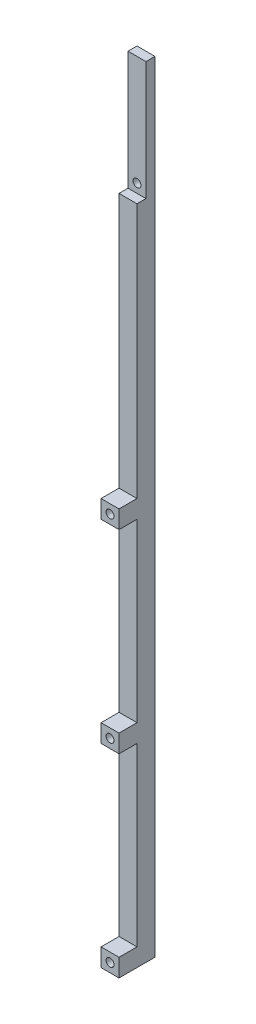
SolidWorks part; units mm, degrees
ref_plane "Front Plane" through (0, 0, 0) normal (0, 0, 1) x (1, 0, 0)
ref_plane "Top Plane" through (0, 0, 0) normal (0, 1, 0) x (1, 0, 0)
ref_plane "Right Plane" through (0, 0, 0) normal (1, 0, 0) x (0, 0, -1)
sketch "Sketch1" plane through (0, 0, 0) normal (0, 1, 0) x (1, 0, 0)
  line L1 (0, 0) -> (6.35, 0)
  line L2 (0, 0) -> (0, 12.7)
  line L3 (0, 12.7) -> (6.35, 12.7)
  line L4 (6.35, 0) -> (6.35, 12.7)
  dimension "D1" = 6.35
  dimension "D2" = 12.7
extrude "Boss-Extrude1" add sketch "Sketch1" along normal blind 275.59
sketch "Sketch2" plane through (0, 0, 0) normal (-1, 0, 0) x (0, 0, 1)
  line L0 (0, 275.59) -> (0, 0) construction
  line L1 (0, 275.59) -> (-9.525, 275.59)
  line L2 (0, 275.59) -> (0, 233.68)
  line L3 (0, 233.68) -> (-9.525, 233.68)
  line L4 (-9.525, 275.59) -> (-9.525, 233.68)
  line L6 (0, 143.51) -> (-6.35, 143.51)
  line L7 (0, 143.51) -> (0, 233.68)
  line L8 (-12.7, 0) -> (0, 0) construction
  line L9 (-6.35, 143.51) -> (-6.35, 233.68)
  line L10 (0, 137.16) -> (-6.35, 137.16)
  line L11 (0, 137.16) -> (0, 74.93)
  line L12 (0, 74.93) -> (-6.35, 74.93)
  line L13 (-6.35, 137.16) -> (-6.35, 74.93)
  line L14 (0, 68.58) -> (-6.35, 68.58)
  line L15 (0, 68.58) -> (0, 6.35)
  line L16 (0, 6.35) -> (-6.35, 6.35)
  line L17 (-6.35, 68.58) -> (-6.35, 6.35)
  line M2 (0, 0) -> (0, 275.59)
  line M3 (0, 275.59) -> (-12.7, 275.59)
  dimension "D1" = 9.525
  dimension "D2" = 6.35
  dimension "D3" = 6.35
  dimension "D4" = 6.35
  dimension "D5" = 6.35
  dimension "D6" = 90.17
  dimension "D7" = 6.35
  dimension "D8" = 62.23
  dimension "D9" = 6.35
  dimension "D10" = 62.23
extrude "Cut-Extrude-Thin1" cut sketch "Sketch2" against normal through all thin contours L4 L3 M3 M2 | L15 L16 L17 L14 | L11 L12 L13 L10 | L9 L6 L7
hole_wizard "#35 (0.11) Diameter Hole1" positions "Sketch5" profile "Sketch4" hole size "#35" standard "ANSI Inch" end condition through all
sketch "Sketch5" plane through (0, 0, 0) normal (0, 0, 1) x (1, 0, 0)
  line L2 (0, 0) -> (6.35, 0) construction
  line L8 (6.35, 74.9299) -> (6.35, 68.5801) construction
  line L9 (6.35, 71.755) -> (0, 71.755) construction
  line L10 (0, 74.9299) -> (0, 68.5801) construction
  line L12 (6.35, 143.5099) -> (6.35, 137.1601) construction
  line L13 (6.35, 140.335) -> (0, 140.335) construction
  line L14 (0, 143.5099) -> (0, 137.1601) construction
  line L19 (3.175, 275.59) -> (3.175, 0) construction
  line L20 (0, 275.59) -> (6.35, 275.59) construction
  point P41 (3.175, 236.855)
  point P43 (3.175, 140.335)
  point P45 (3.175, 71.755)
  point P47 (3.175, 3.175)
  dimension "D1" = 3.175
  dimension "D2" = 71.755
  dimension "D3" = 140.335
  dimension "D4" = 236.855
sketch "Sketch4" plane through (3.175, 236.855, 0) normal (1, 0, 0) x (0, -1, 0)
  line L0 (0, 0) -> (0, 12.7)
  line L1 (0, 12.7) -> (1.397, 12.7)
  line L2 (1.397, 12.7) -> (1.397, 0)
  line L5 (1.397, 0) -> (0, 0)
  line L11 (0, -6.35) -> (0, 107.95) construction
  dimension "Thru Hole Dia." = 2.794
  dimension "Thru Hole Depth" = 12.7
